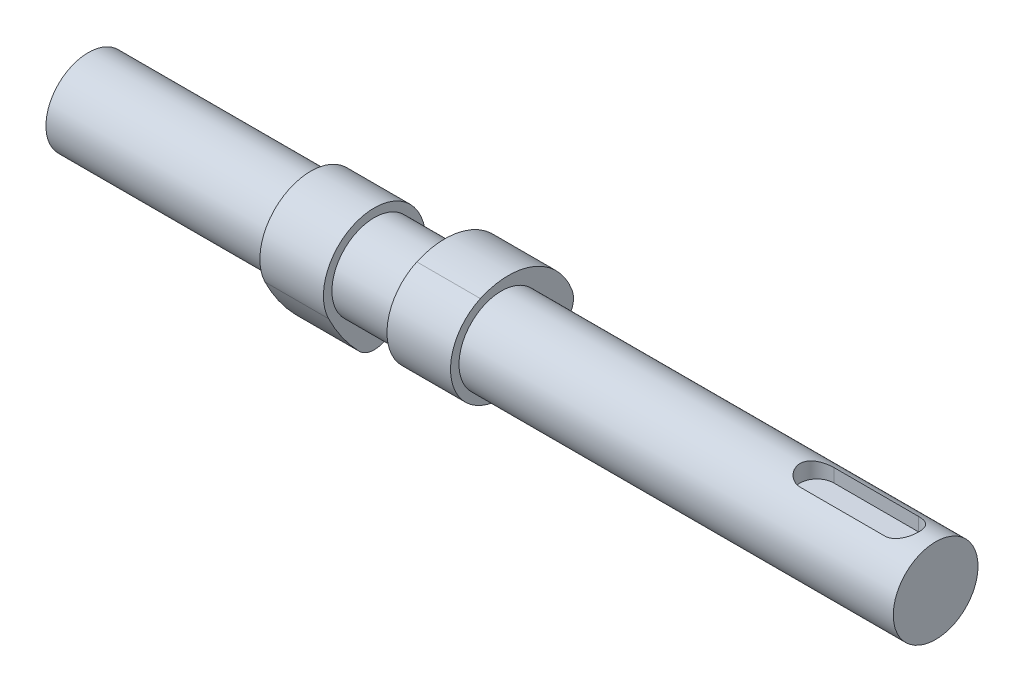
SolidWorks part; units mm, degrees
ref_plane "Front Plane" through (0, 0, 0) normal (0, 0, 1) x (1, 0, 0)
ref_plane "Top Plane" through (0, 0, 0) normal (0, 1, 0) x (1, 0, 0)
ref_plane "Right Plane" through (0, 0, 0) normal (1, 0, 0) x (0, 0, -1)
sketch "Sketch1" plane through (0, 0, 0) normal (1, 0, 0) x (0, 0, -1)
  circle A0 centre (0, 0) radius 10
  dimension "D1" = 20
extrude "Boss-Extrude1" add sketch "Sketch1" against normal blind 75 and the other way blind 125
sketch "Sketch2" plane through (0, 0, 0) normal (1, 0, 0) x (0, 0, -1)
  line L0 (0, 0) -> (14.015, 0) construction
  arc A0 (-4.9508, 10.9311) -> (5.2781, -10.7769) centre (0, 0) ccw
  arc A1 (15.5071, -3.5923) -> (16.747, 1.6562) centre (12.0293, 0) ccw
  arc A2 (-4.9508, 10.9311) -> (16.747, 1.6562) centre (1.6503, -3.6437) cw
  arc A3 (5.2781, -10.7769) -> (15.5071, -3.5923) centre (-12.3157, 25.1461) ccw
  dimension "D1" = 24
  dimension "D2" = 10
  dimension "D3" = 16
  dimension "D4" = 40
  dimension "D5" = 12.5
extrude "Boss-Extrude2" add sketch "Sketch2" along normal mid plane 15 from offset 15 separate body
pattern_linear "LPattern1" count 2 spacing 30 along (-1, 0, 0) of "Boss-Extrude2"
move or copy body "Body-Move/Copy1" bodies to move or copy 104 copy no rotation origin (0, 0, 0) rotation axis (-1, 0, 0) rotation angle 90
ref_plane "Plane1" through (0, 10, 0) normal (0, 1, 0) x (1, 0, 0)
sketch "Sketch3" plane through (0, 10, 0) normal (0, 1, 0) x (1, 0, 0)
  line L0 (0, 0) -> (197.7963, 0) construction
  line L1 (97, 0) -> (117, 0) construction
  line L2 (97, 4) -> (117, 4)
  line L3 (97, -4) -> (117, -4)
  line L4 (125, -10) -> (125, 10) construction
  arc A0 (97, 4) -> (97, -4) centre (97, 0) ccw
  arc A1 (117, -4) -> (117, 4) centre (117, 0) ccw
  point P5 (107, 0)
  dimension "D3" = 4
  dimension "D1" = 20
  dimension "D2" = 8
extrude "Cut-Extrude1" cut sketch "Sketch3" against normal blind 4
